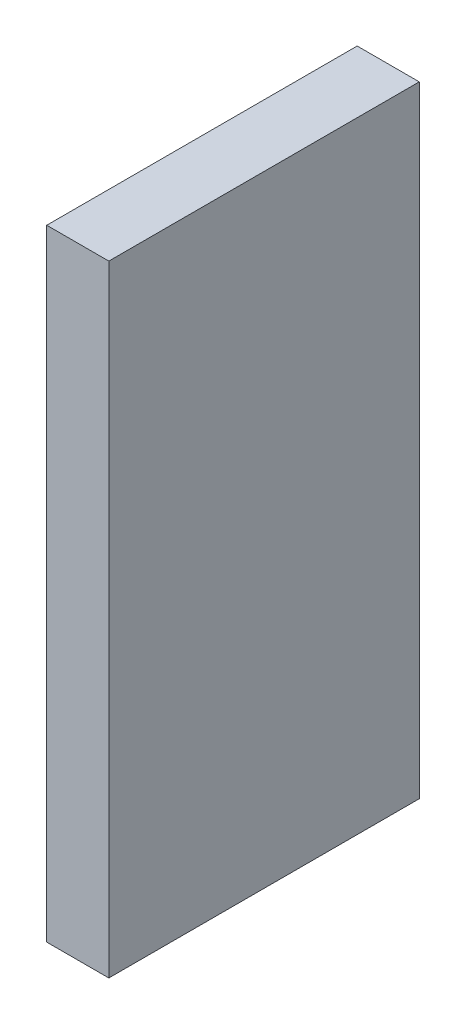
SolidWorks part; units mm, degrees
ref_plane "Alzado" through (0, 0, 0) normal (0, 0, 1) x (1, 0, 0)
ref_plane "Planta" through (0, 0, 0) normal (0, 1, 0) x (1, 0, 0)
ref_plane "Vista lateral" through (0, 0, 0) normal (1, 0, 0) x (0, 0, -1)
sketch "Croquis1" plane through (0, 0, 0) normal (1, 0, 0) x (0, 0, -1)
  line L1 (-30, 60) -> (30, 60)
  line L2 (-30, 60) -> (-30, -60)
  line L3 (-30, -60) -> (30, -60)
  line L4 (30, 60) -> (30, -60)
  line L5 (-30, 60) -> (30, -60) construction
  line L6 (-30, -60) -> (30, 60) construction
  point P0 (0, 0)
  dimension "D1" = 120
  dimension "D2" = 60
extrude "Saliente-Extruir1" add sketch "Croquis1" along normal blind 12
